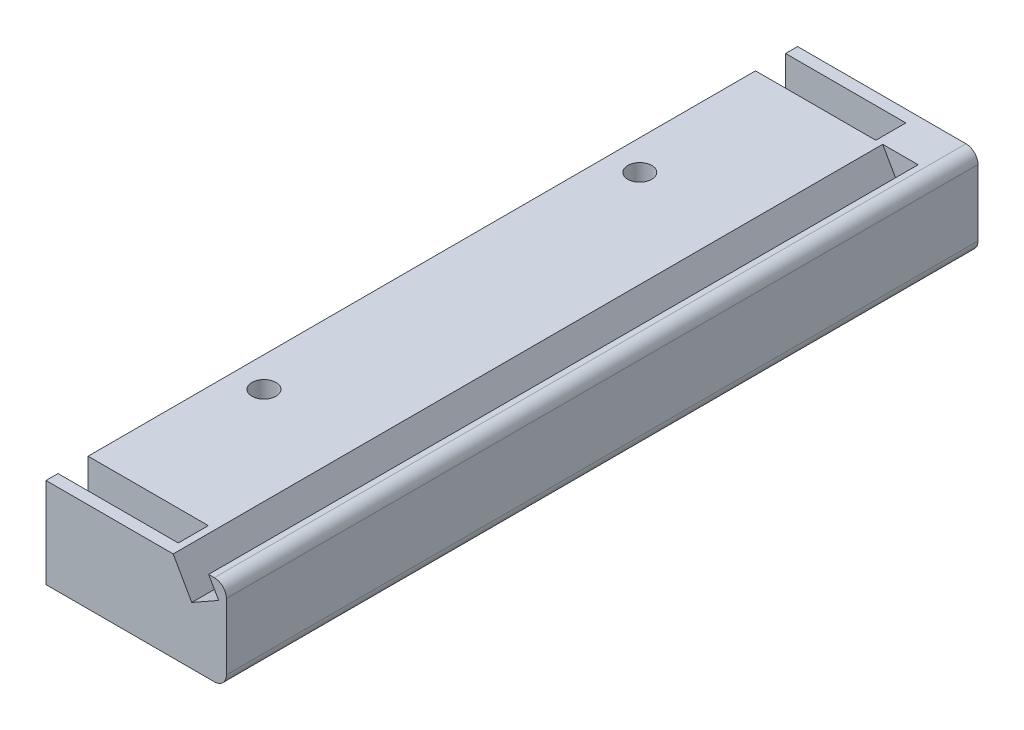
SolidWorks part; units mm, degrees
ref_plane "Alzado" through (0, 0, 0) normal (0, 0, 1) x (1, 0, 0)
ref_plane "Planta" through (0, 0, 0) normal (0, 1, 0) x (1, 0, 0)
ref_plane "Vista lateral" through (0, 0, 0) normal (1, 0, 0) x (0, 0, -1)
sketch "Croquis1" plane through (0, 0, 0) normal (0, 0, 1) x (1, 0, 0)
  line L0 (0, 0) -> (0, 15)
  line L1 (0, 15) -> (28, 15)
  line L2 (0, 0) -> (28, 0)
  line L3 (30, 13) -> (30, 2)
  line L4 (0, 7.5) -> (30, 7.5) construction
  line L6 (0, 10) -> (20, 10)
  line L7 (0, 10) -> (0, 5)
  line L8 (0, 5) -> (20, 5)
  line L9 (20, 10) -> (20, 5)
  arc A0 (28, 0) -> (30, 2) centre (28, 2) ccw
  arc A1 (28, 15) -> (30, 13) centre (28, 13) cw
  point P7 (30, 0)
  dimension "D3" = 2
  dimension "D1" = 15
  dimension "D2" = 30
  dimension "D4" = 20
  dimension "D5" = 5
  dimension "D6" = 5
extrude "Saliente-Extruir1" add sketch "Croquis1" along normal blind 111 contours L4 L9 L8 L0 L2 A0 L3 | L9 L4 L3 A1 L1 L0 L6
sketch "Croquis2" plane through (0, 0, 111) normal (0, 0, 1) x (1, 0, 0)
  line L0 (20, 10) -> (20, 15)
  line L8 (30, 2) -> (30, 13)
  line L9 (28, 15) -> (0, 15)
  line L10 (0, 15) -> (0, 10)
  line L11 (0, 10) -> (20, 10)
  line L12 (20, 10) -> (20, 5)
  line L13 (20, 5) -> (0, 5)
  line L14 (0, 5) -> (0, 0)
  line L15 (0, 0) -> (28, 0)
  line L16 (30, 2) -> (30, 13)
  line L17 (28, 15) -> (0, 15)
  line L18 (0, 15) -> (0, 10)
  line L19 (0, 10) -> (20, 10)
  line L20 (20, 10) -> (20, 5)
  line L21 (20, 5) -> (0, 5)
  line L22 (0, 5) -> (0, 0)
  line L23 (0, 0) -> (28, 0)
  arc A2 (30, 13) -> (28, 15) centre (28, 13) ccw
  arc A3 (28, 0) -> (30, 2) centre (28, 2) ccw
  arc A4 (30, 13) -> (28, 15) centre (28, 13) ccw
  arc A5 (28, 0) -> (30, 2) centre (28, 2) ccw
  line M11 (30, 2) -> (30, 13)
  arc M12 (30, 13) -> (28, 15) centre (28, 13) ccw
  line M13 (28, 15) -> (0, 15)
  line M16 (20, 10) -> (20, 5)
  line M17 (20, 5) -> (0, 5)
  line M18 (0, 5) -> (0, 0)
  line M19 (0, 0) -> (28, 0)
  arc M20 (28, 0) -> (30, 2) centre (28, 2) ccw
  dimension "D1" = 0
extrude "Saliente-Extruir2" add sketch "Croquis2" along normal blind 5 contours L0 M16 M17 M18 M19 M20 M11 M12 M13
sketch "Croquis3" plane through (0, 0, 116) normal (0, 0, 1) x (1, 0, 0)
  line L0 (20, 15) -> (20, 5) construction
  line L1 (20, 5) -> (0, 5) construction
  line L2 (0, 5) -> (0, 0) construction
  line L3 (0, 0) -> (28, 0) construction
  line L6 (0, 10) -> (20, 10) construction
  line L7 (20, 10) -> (20, 15) construction
  line L8 (20, 15) -> (0, 15) construction
  line L9 (0, 15) -> (0, 10) construction
  line L10 (20, 15) -> (20, 5)
  line L11 (20, 5) -> (0, 5)
  line L12 (0, 5) -> (0, 0)
  line L13 (0, 0) -> (28, 0)
  line L15 (11, 15) -> (20, 15)
  line L16 (0, 10) -> (20, 10)
  line L17 (20, 10) -> (20, 15)
  line L18 (20, 15) -> (0, 15)
  line L19 (0, 15) -> (0, 10)
  line L20 (0, 10) -> (0, 5)
  line L26 (20, 15) -> (20, 5)
  line L27 (20, 5) -> (0, 5)
  line L28 (0, 5) -> (0, 0)
  line L29 (0, 0) -> (28, 0)
  line L30 (30, 2) -> (30, 13)
  line L31 (20, 15) -> (20, 5)
  line L32 (20, 5) -> (0, 5)
  line L33 (0, 5) -> (0, 0)
  line L34 (0, 0) -> (28, 0)
  line L35 (30, 2) -> (30, 13)
  line L37 (28, 15) -> (20, 15)
  line L38 (28, 15) -> (20, 15)
  arc A6 (28, 0) -> (30, 2) centre (28, 2) ccw
  arc A7 (30, 13) -> (28, 15) centre (28, 13) ccw
  arc A8 (28, 0) -> (30, 2) centre (28, 2) ccw
  arc A9 (30, 13) -> (28, 15) centre (28, 13) ccw
  line M1 (20, 15) -> (20, 5)
  line M2 (20, 5) -> (0, 5)
  line M3 (0, 5) -> (0, 0)
  line M4 (0, 0) -> (28, 0)
  arc M5 (28, 0) -> (30, 2) centre (28, 2) ccw
  line M6 (30, 2) -> (30, 13)
  arc M7 (30, 13) -> (28, 15) centre (28, 13) ccw
  line M8 (28, 15) -> (20, 15)
  dimension "D1" = 0
extrude "Saliente-Extruir3" add sketch "Croquis3" along normal blind 2 contours L18 L19 L16 M1 | L10 M8 M1 M2 M3 M4 M5 M6 M7 | L16 L20 L10 M2
sketch "Croquis4" plane through (0, 0, 0) normal (0, 0, -1) x (-1, 0, 0)
  line L0 (-20, 10) -> (-20, 15)
  line L8 (-30, 13) -> (-30, 2)
  line L9 (-28, 0) -> (0, 0)
  line L10 (0, 0) -> (0, 5)
  line L11 (0, 5) -> (-20, 5)
  line L12 (-20, 5) -> (-20, 10)
  line L13 (-20, 10) -> (0, 10)
  line L14 (0, 10) -> (0, 15)
  line L15 (0, 15) -> (-28, 15)
  line L16 (-30, 13) -> (-30, 2)
  line L17 (-28, 0) -> (0, 0)
  line L18 (0, 0) -> (0, 5)
  line L19 (0, 5) -> (-20, 5)
  line L20 (-20, 5) -> (-20, 10)
  line L21 (-20, 10) -> (0, 10)
  line L22 (0, 10) -> (0, 15)
  line L23 (0, 15) -> (-28, 15)
  arc A2 (-30, 2) -> (-28, 0) centre (-28, 2) ccw
  arc A3 (-28, 15) -> (-30, 13) centre (-28, 13) ccw
  arc A4 (-30, 2) -> (-28, 0) centre (-28, 2) ccw
  arc A5 (-28, 15) -> (-30, 13) centre (-28, 13) ccw
  line M11 (-30, 13) -> (-30, 2)
  arc M12 (-30, 2) -> (-28, 0) centre (-28, 2) ccw
  line M13 (-28, 0) -> (0, 0)
  line M14 (0, 0) -> (0, 5)
  line M15 (0, 5) -> (-20, 5)
  line M16 (-20, 5) -> (-20, 10)
  line M19 (0, 15) -> (-28, 15)
  arc M20 (-28, 15) -> (-30, 13) centre (-28, 13) ccw
  dimension "D1" = 0
extrude "Saliente-Extruir4" add sketch "Croquis4" along normal blind 5 contours L0 M16 M19 M20 M11 M12 M13 M14 M15
sketch "Croquis5" plane through (0, 0, -5) normal (0, 0, -1) x (-1, 0, 0)
  line L3 (0, 15) -> (-20, 15) construction
  line L7 (0, 15) -> (-20, 15) construction
  line L17 (0, 15) -> (-11, 15)
  line L21 (0, 15) -> (-11, 15)
  line L30 (-28, 0) -> (0, 0) construction
  line L31 (0, 0) -> (0, 5) construction
  line L35 (0, 5) -> (0, 15) construction
  line L38 (0, 10) -> (0, 15) construction
  line L41 (-28, 0) -> (0, 0)
  line L42 (0, 0) -> (0, 5)
  line L46 (0, 5) -> (0, 15)
  line L47 (0, 15) -> (-20, 15)
  line L50 (0, 10) -> (0, 15)
  line L51 (0, 15) -> (-20, 15)
  line L52 (0, 10) -> (0, 5)
  line L53 (-20, 15) -> (-20, 5) construction
  line L54 (-20, 5) -> (0, 5) construction
  line L55 (0, 5) -> (0, 15) construction
  line L56 (0, 15) -> (-20, 15) construction
  line L57 (-20, 15) -> (-20, 10) construction
  line L58 (-20, 10) -> (0, 10) construction
  line L59 (-20, 5) -> (-20, 15) construction
  line L60 (-20, 15) -> (-28, 15) construction
  line L61 (-30, 13) -> (-30, 2) construction
  line L62 (0, 5) -> (-20, 5) construction
  line L63 (-20, 15) -> (-20, 5)
  line L64 (-20, 5) -> (0, 5)
  line L65 (0, 5) -> (0, 15)
  line L66 (0, 15) -> (-20, 15)
  line L67 (-20, 15) -> (-20, 10)
  line L68 (-20, 10) -> (0, 10)
  line L69 (0, 10) -> (0, 15)
  line L70 (0, 15) -> (-20, 15)
  line L71 (-20, 5) -> (-20, 15)
  line L72 (-20, 15) -> (-28, 15)
  line L73 (-30, 13) -> (-30, 2)
  line L74 (-28, 0) -> (0, 0)
  line L75 (0, 0) -> (0, 5)
  line L76 (0, 5) -> (-20, 5)
  arc A8 (-28, 15) -> (-30, 13) centre (-28, 13) ccw construction
  arc A9 (-30, 2) -> (-28, 0) centre (-28, 2) ccw construction
  arc A10 (-28, 15) -> (-30, 13) centre (-28, 13) ccw
  arc A11 (-30, 2) -> (-28, 0) centre (-28, 2) ccw
extrude "Saliente-Extruir5" add sketch "Croquis5" along normal blind 2
sketch "Croquis6" plane through (0, 0, 0) normal (0, -1, 0) x (1, 0, 0)
  line L0 (5, -7) -> (5, 118) construction
  line L3 (0, 118) -> (0, -7) construction
  circle A0 centre (5, 24.25) radius 2
  circle A1 centre (5, 86.75) radius 2
  point P10 (5, 55.5)
  dimension "D1" = 4
  dimension "D2" = 4
  dimension "D3" = 31.25
  dimension "D4" = 31.25
  dimension "D5" = 5
extrude "Cortar-Extruir1" cut sketch "Croquis6" against normal blind 41
sketch "Croquis7" plane through (0, 0, 0) normal (0, -1, 0) x (-1, 0, 0)
  circle A0 centre (-5, -24.25) radius 4
  circle A1 centre (-5, -86.75) radius 4
  dimension "D1" = 8
  dimension "D2" = 8
extrude "Cortar-Extruir2" cut sketch "Croquis7" against normal blind 4
sketch "Croquis8" plane through (0, 15, 0) normal (0, 1, 0) x (1, 0, 0)
  line L0 (0, 5) -> (20, 5) construction
  line L1 (22, 5) -> (28, 5)
  line L2 (22, 5) -> (22, 0)
  line L3 (22, 0) -> (28, 0)
  line L4 (28, 5) -> (28, 0)
  line L5 (28, -118) -> (28, 7) construction
  line L6 (0, -111) -> (20, -111) construction
  line L7 (22, -111) -> (28, -111)
  line L8 (22, -111) -> (22, -116.1119)
  line L9 (22, -116.1119) -> (28, -116.1119)
  line L10 (28, -111) -> (28, -116.1119)
  dimension "D1" = 6
  dimension "D2" = 5.1119
  dimension "D3" = 6
extrude "Cortar-Extruir3" [suppressed] cut sketch "Croquis8" against normal blind 5
sketch "Croquis9" plane through (0, 0, 118) normal (0, 0, 1) x (1, 0, 0)
  line L0 (27.0465, 15) -> (28.7193, 12.0857)
  line L1 (28.7193, 12.0857) -> (24.2394, 9.549)
  line L2 (24.2394, 9.549) -> (21.1528, 15)
  line L3 (28, 15) -> (0, 15) construction
  line L4 (27.0465, 15) -> (21.1528, 15)
extrude "Cortar-Extruir4" cut sketch "Croquis9" against normal up to surface (118 mm away) up to face at (10, 12.5, 0)
